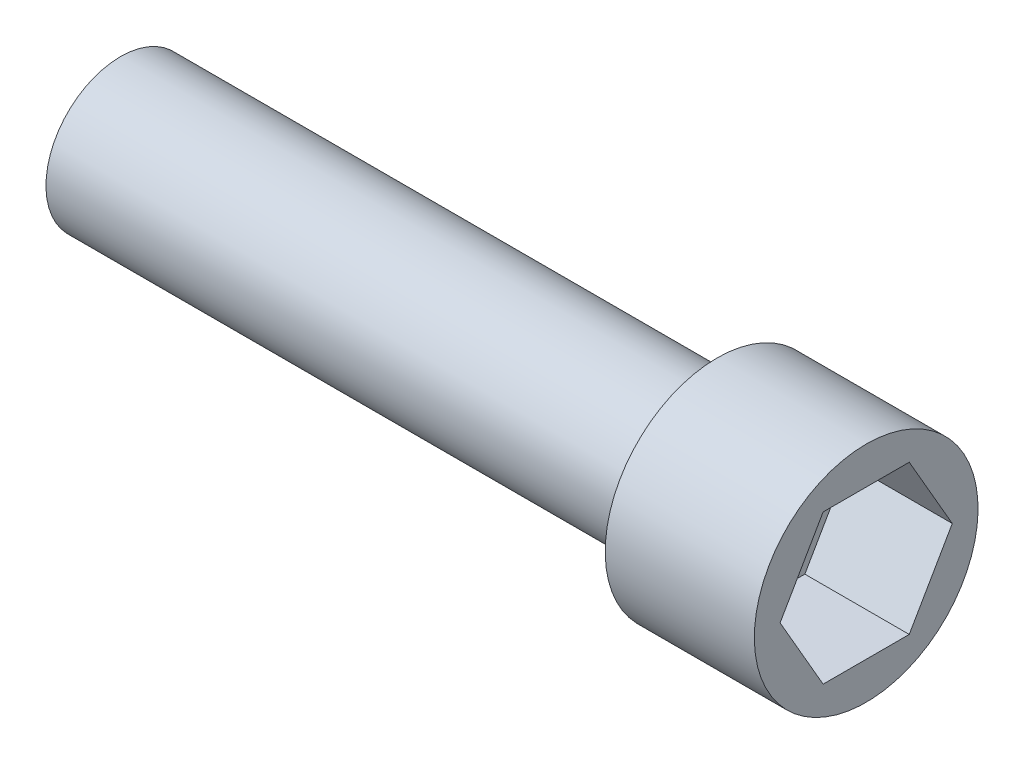
SolidWorks part; units mm, degrees
ref_plane "Front Plane" through (0, 0, 0) normal (0, 0, 1) x (1, 0, 0)
ref_plane "Top Plane" through (0, 0, 0) normal (0, 1, 0) x (1, 0, 0)
ref_plane "Right Plane" through (0, 0, 0) normal (1, 0, 0) x (0, 0, -1)
sketch "Sketch1" plane through (0, 0, 0) normal (0, 0, 1) x (1, 0, 0)
  line L0 (-25, 5) -> (15, 5)
  line L1 (15, 5) -> (15, 7.5)
  line L2 (15, 7.5) -> (25, 7.5)
  line L3 (25, 7.5) -> (25, 0)
  line L4 (25, 0) -> (-25, 0)
  line L5 (-25, 0) -> (-25, 5)
  dimension "D1" = 40
  dimension "D2" = 5
  dimension "D3" = 10
  dimension "D4" = 25
  dimension "D5" = 2.5
  dimension "D6" = 7.5
revolve "Revolve1" add sketch "Sketch1" angle 360 about L4
sketch "Sketch2" plane through (25, 0, 0) normal (1, 0, 0) x (0, 0, -1)
  line L1 (5.7735, 0) -> (2.8868, 5)
  line L2 (2.8868, 5) -> (-2.8868, 5)
  line L3 (-2.8868, 5) -> (-5.7735, 0)
  line L4 (-5.7735, 0) -> (-2.8868, -5)
  line L5 (-2.8868, -5) -> (2.8868, -5)
  line L6 (2.8868, -5) -> (5.7735, 0)
  circle A0 centre (0, 0) radius 5 construction
  circle A1 centre (0, 0) radius 7.5 construction
  point P11 (0, 0)
  point P12 (0, 0)
  dimension "D1" = 10
extrude "Cut-Extrude1" cut sketch "Sketch2" against normal blind 7
